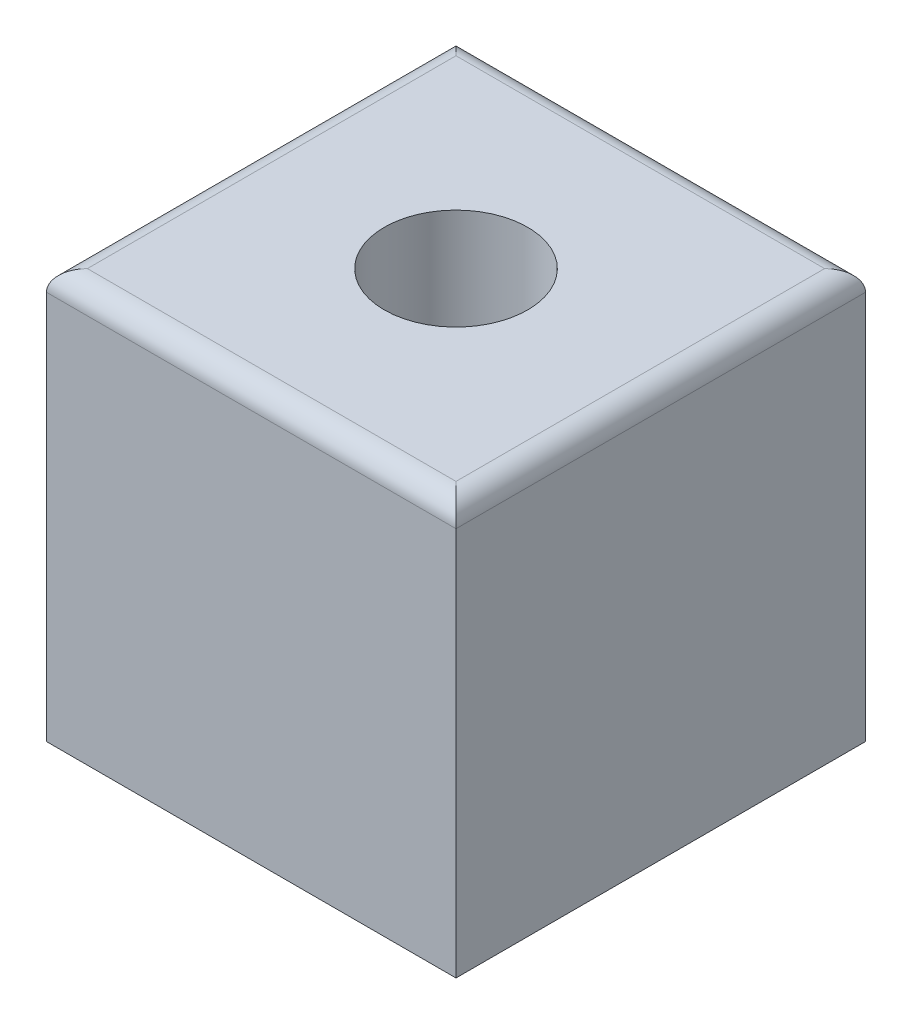
SolidWorks part; units mm, degrees
material "ASTM A36 Steel"
ref_plane "Front Plane" through (0, 0, 0) normal (0, 0, 1) x (1, 0, 0)
ref_plane "Top Plane" through (0, 0, 0) normal (0, 1, 0) x (1, 0, 0)
ref_plane "Right Plane" through (0, 0, 0) normal (1, 0, 0) x (0, 0, -1)
sketch "Sketch2" plane through (0, 0, 0) normal (0, 0, 1) x (1, 0, 0)
  line L1 (-127, 127) -> (127, 127)
  line L2 (-127, 127) -> (-127, -127)
  line L3 (-127, -127) -> (127, -127)
  line L4 (127, 127) -> (127, -127)
  line L5 (-127, 127) -> (127, -127) construction
  line L6 (-127, -127) -> (127, 127) construction
  point P0 (0, 0)
  dimension "D1" = 254
extrude "Boss-Extrude1" add sketch "Sketch2" along normal mid plane 254 contours L1 L4 L3 L2
sketch "Sketch3" plane through (0, 127, 0) normal (0, 1, 0) x (1, 0, 0)
  circle A0 centre (0, 0) radius 44.45
  dimension "D1" = 88.9
extrude "Cut-Extrude1" cut sketch "Sketch3" against normal blind 82.55
fillet "Fillet1" radius 12.7 4 edges at (127, 127, 0) (-127, 127, 0) (0, 127, -127) (0, 127, 127)
